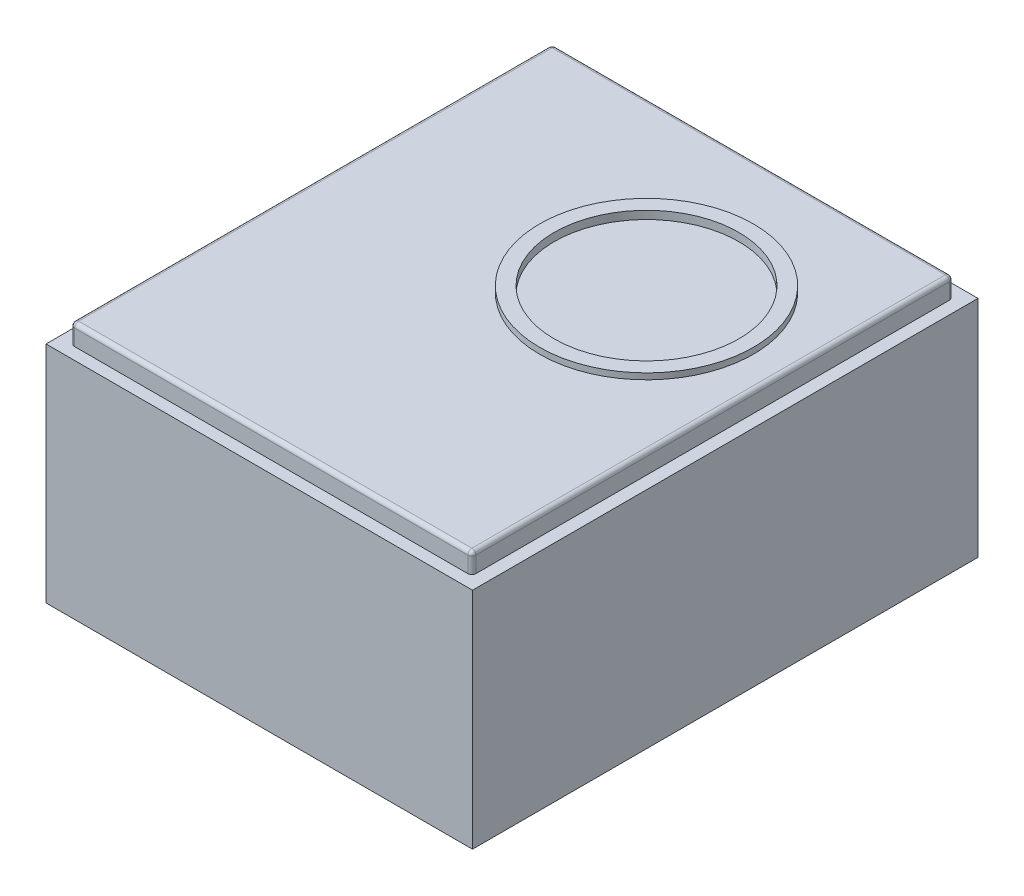
SolidWorks part; units mm, degrees
ref_plane "Front Plane" through (0, 0, 0) normal (0, 0, 1) x (1, 0, 0)
ref_plane "Top Plane" through (0, 0, 0) normal (0, 1, 0) x (1, 0, 0)
ref_plane "Right Plane" through (0, 0, 0) normal (1, 0, 0) x (0, 0, -1)
sketch "Sketch1" plane through (0, 0, 0) normal (0, 1, 0) x (1, 0, 0)
  line L1 (-135, -160) -> (135, -160)
  line L2 (-135, -160) -> (-135, 160)
  line L3 (-135, 160) -> (135, 160)
  line L4 (135, -160) -> (135, 160)
  line L5 (-135, -160) -> (135, 160) construction
  line L6 (-135, 160) -> (135, -160) construction
  point P0 (0, 0)
  dimension "D1" = 270
  dimension "D2" = 320
extrude "Boss-Extrude1" add sketch "Sketch1" along normal blind 142
sketch "Sketch3" plane through (0, 142, 0) normal (0, 1, 0) x (1, 0, 0)
  line L1 (-127, 152.4) -> (127, 152.4)
  line L2 (-127, 152.4) -> (-127, -152.4)
  line L3 (-127, -152.4) -> (127, -152.4)
  line L4 (127, 152.4) -> (127, -152.4)
  line L5 (-127, 152.4) -> (127, -152.4) construction
  line L6 (-127, -152.4) -> (127, 152.4) construction
  point P0 (0, 0)
extrude "Boss-Extrude3" add sketch "Sketch3" along normal blind 12.7
fillet "Fillet1" radius 2.54 4 edges at (127, 148.35, -152.4) (-127, 148.35, -152.4) (-127, 148.35, 152.4) (127, 148.35, 152.4)
fillet "Fillet2" radius 2.54 8 edges at (-126.2561, 154.7, 151.6561) (-127, 154.7, 0) (-126.2561, 154.7, -151.6561) (0, 154.7, -152.4) (126.2561, 154.7, -151.6561) (127, 154.7, 0) (126.2561, 154.7, 151.6561) (0, 154.7, 152.4)
sketch "Sketch7" plane through (0, 154.7, 0) normal (0, 1, 0) x (1, 0, 0)
  circle A0 centre (39.5976, 45.5507) radius 67.6786
  point P2 (-43.2634, 89.1674)
  point P3 (-26.4164, 69.3061)
  point P4 (0, 0)
  point P5 (-11.564, 68.6642)
  point P6 (39.5976, 45.5507)
  point P7 (0, 0)
extrude "Boss-Extrude4" add sketch "Sketch7" along normal blind 3.81
sketch "Sketch8" plane through (0, 158.51, 0) normal (0, 1, 0) x (1, 0, 0)
  circle A0 centre (39.5976, 45.5507) radius 58.425
  point P2 (-42.0964, 89.8817)
  point P3 (0, 0)
  point P4 (-43.6263, 88.9144)
  point P5 (39.5976, 45.5507)
extrude "Cut-Extrude2" cut sketch "Sketch8" against normal blind 5.08
